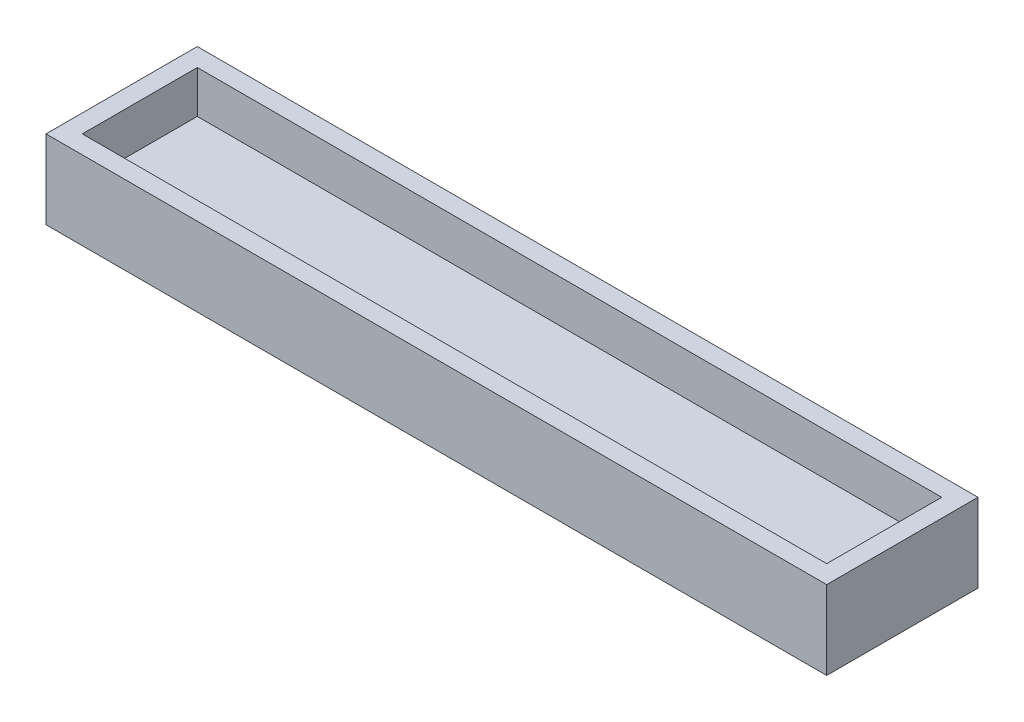
SolidWorks part; units mm, degrees
ref_plane "Front Plane" through (0, 0, 0) normal (0, 0, 1) x (1, 0, 0)
ref_plane "Top Plane" through (0, 0, 0) normal (0, 1, 0) x (1, 0, 0)
ref_plane "Right Plane" through (0, 0, 0) normal (1, 0, 0) x (0, 0, -1)
sketch "Sketch1" plane through (0, 0, 0) normal (0, 1, 0) x (1, 0, 0)
  line L1 (0, 0) -> (123, 0)
  line L2 (0, 0) -> (0, 19)
  line L3 (0, 19) -> (123, 19)
  line L4 (123, 0) -> (123, 19)
  dimension "D1" = 123
  dimension "D2" = 19
extrude "Boss-Extrude1" add sketch "Sketch1" along normal blind 6
sketch "Sketch2" plane through (0, 0, 0) normal (0, -1, 0) x (1, 0, 0)
  line L0 (-3, 3) -> (-3, -22)
  line L1 (0, 0) -> (123, 0)
  line L2 (0, 0) -> (0, -19)
  line L3 (0, -19) -> (123, -19)
  line L4 (123, 0) -> (123, -19)
  line L5 (-3, -22) -> (126, -22)
  line L6 (126, 3) -> (126, -22)
  line L7 (-3, 3) -> (126, 3)
  dimension "D1" = 3
extrude "Boss-Extrude3" add sketch "Sketch2" against normal offset from surface (13 mm away) 7 up to face at (61.5, 6, -9.5) offset beyond the face yes
